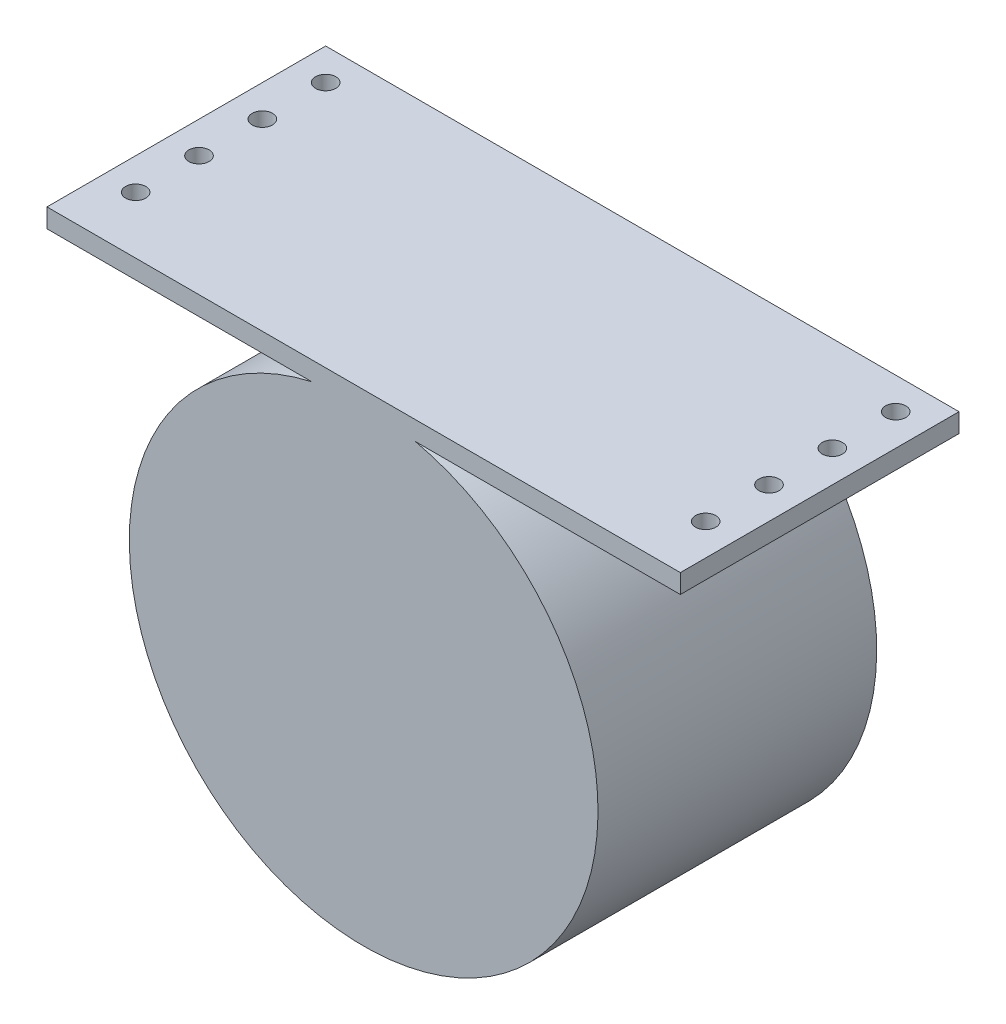
SolidWorks part; units mm, degrees
ref_plane "正面" through (0, 0, 0) normal (0, 0, 1) x (1, 0, 0)
ref_plane "平面" through (0, 0, 0) normal (0, 1, 0) x (1, 0, 0)
ref_plane "右側面" through (0, 0, 0) normal (1, 0, 0) x (0, 0, -1)
sketch "ｽｹｯﾁ1" plane through (0, 0, 0) normal (0, 0, 1) x (1, 0, 0)
  line L1 (-55.7953, 40.2716) -> (44.2047, 40.2716)
  line L2 (-55.7953, 40.2716) -> (-55.7953, 43.2716)
  line L3 (-55.7953, 43.2716) -> (44.2047, 43.2716)
  line L4 (44.2047, 40.2716) -> (44.2047, 43.2716)
  circle A0 centre (-5.7953, 4.1854) radius 34
  circle A1 centre (-5.7953, 4.1854) radius 37
  dimension "D1" = 3
  dimension "D2" = 3
  dimension "D4" = 50
  dimension "D3" = 100
extrude "ﾎﾞｽ - 押し出し1" add sketch "ｽｹｯﾁ1" along normal blind 44 contours A1 | L2 L1 L4 L3
sketch "ｽｹｯﾁ2" plane through (0, 0, 0) normal (0, 0, -1) x (-1, 0, 0)
  circle A0 centre (5.7953, 4.1854) radius 34
  circle A1 centre (5.7953, 4.1854) radius 37 construction
  dimension "D1" = 0
extrude "ｶｯﾄ - 押し出し1" cut sketch "ｽｹｯﾁ2" against normal blind 40
sketch3d "3Dｽｹｯﾁ1"
  point P0 (-42.7365, 6.2721, 16.4878)
sketch3d "3Dｽｹｯﾁ2"
  point P0 (11.9158, -24.8373, 10.4886)
sketch "ｽｹｯﾁ4" plane through (0, 43.2716, 0) normal (0, 1, 0) x (1, 0, 0)
  line L0 (-55.7953, -44) -> (-55.7953, 0) construction
  line L1 (-55.7953, 0) -> (44.2047, 0) construction
  circle A0 centre (-50.7953, -5) radius 1.6
  circle A1 centre (-50.7953, -15) radius 1.6
  circle A2 centre (-50.7953, -25) radius 1.6
  circle A3 centre (-50.7953, -35) radius 1.6
  dimension "D1" = 5
  dimension "D2" = 5
  dimension "D3" = 3.2
  dimension "D4" = 4
extrude "ｶｯﾄ - 押し出し2" cut sketch "ｽｹｯﾁ4" against normal blind 10
pattern_linear "直線ﾊﾟﾀｰﾝ1" count 2 spacing 90 along (1, 0, 0) of "ｶｯﾄ - 押し出し2"
